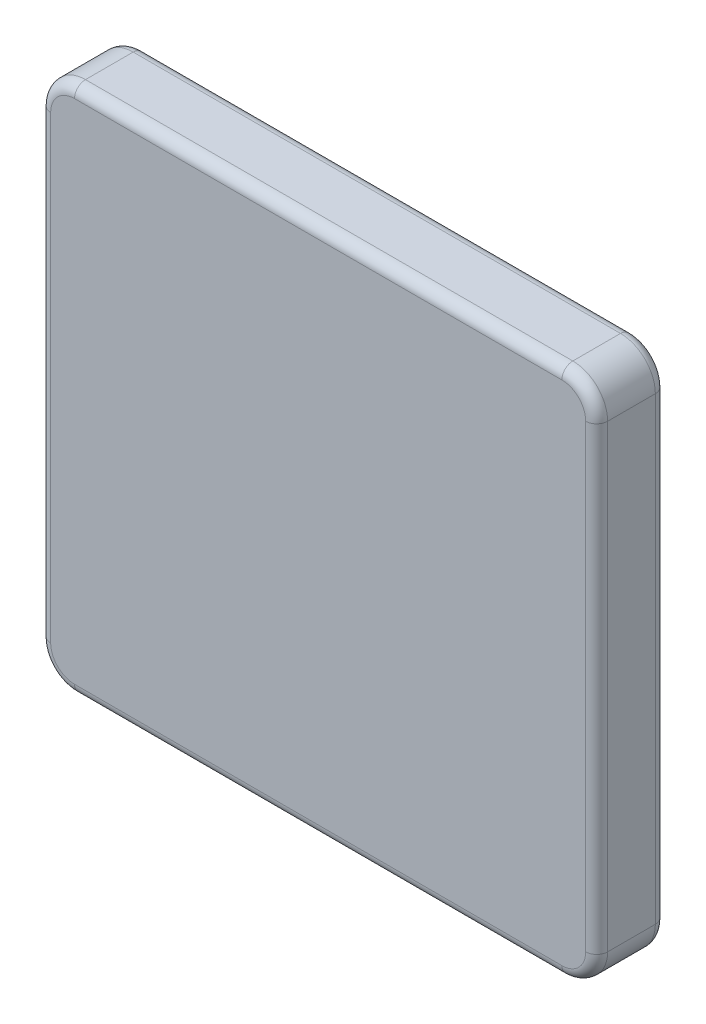
SolidWorks part; units mm, degrees
ref_plane "Front Plane" through (0, 0, 0) normal (0, 0, 1) x (1, 0, 0)
ref_plane "Top Plane" through (0, 0, 0) normal (0, 1, 0) x (1, 0, 0)
ref_plane "Right Plane" through (0, 0, 0) normal (1, 0, 0) x (0, 0, -1)
sketch "Sketch1" plane through (0, 0, 0) normal (0, 0, 1) x (1, 0, 0)
  line L1 (0, 0) -> (2032, 0)
  line L2 (0, 0) -> (0, 1930.4)
  line L3 (0, 1930.4) -> (2032, 1930.4)
  line L4 (2032, 0) -> (2032, 1930.4)
  dimension "D1" = 1930.4
  dimension "D2" = 2032
extrude "Boss-Extrude1" add sketch "Sketch1" along normal blind 254
fillet "Fillet1" radius 127 4 edges at (0, 1930.4, 127) (0, 0, 127) (2032, 0, 127) (2032, 1930.4, 127)
fillet "Fillet2" radius 40 16 edges at (37.1974, 1893.2026, 254) (1016, 1930.4, 254) (1994.8026, 1893.2026, 254) (2032, 965.2, 254) (1994.8026, 37.1974, 254) (1016, 0, 254) (37.1974, 37.1974, 254) (37.1974, 1893.2026, 0) (1016, 1930.4, 0) (1994.8026, 1893.2026, 0) (2032, 965.2, 0) (1994.8026, 37.1974, 0) (1016, 0, 0) (37.1974, 37.1974, 0) (0, 965.2, 254) (0, 965.2, 0)
